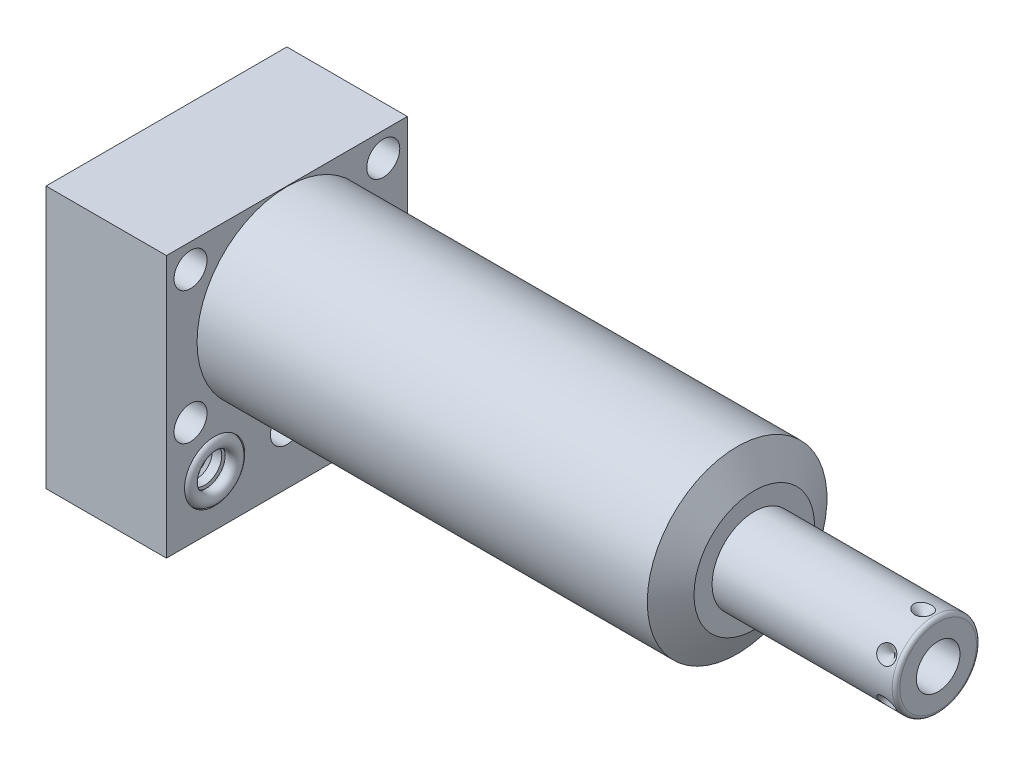
SolidWorks part; units mm, degrees
material "Alloy Steel"
ref_plane "Front Plane" through (0, 0, 0) normal (0, 0, 1) x (1, 0, 0)
ref_plane "Top Plane" through (0, 0, 0) normal (0, 1, 0) x (1, 0, 0)
ref_plane "Right Plane" through (0, 0, 0) normal (1, 0, 0) x (0, 0, -1)
ref_plane "Plane1" through (0, 0, 0) normal (1, 0, 0) x (0, 0, -1)
sketch "Sketch1" plane through (0, 0, 0) normal (1, 0, 0) x (0, 0, -1)
  line L0 (-31.75, 23.8252) -> (-31.75, -45.2628)
  line L1 (-31.75, -45.2628) -> (31.75, -45.2628)
  line L2 (31.75, -45.2628) -> (31.75, 23.8252)
  line L3 (31.75, 23.8252) -> (-31.75, 23.8252)
  line L4 (0, -55.6514) -> (0, 27.6098) construction
  dimension "D1" = 63.5
  dimension "D2" = 69.088
  dimension "D3" = 23.8252
extrude "Extrude1" add sketch "Sketch1" along normal blind 123.19 and the other way blind 31.75
ref_plane "Plane2" through (0, 0, 0) normal (1, 0, 0) x (0, 0, -1)
sketch "Sketch2" plane through (0, 0, 0) normal (1, 0, 0) x (0, 0, -1)
  line L0 (-26.0541, 0) -> (26.0541, 0) construction
  line L5 (31.75, 23.8252) -> (-31.75, 23.8252)
  line L6 (-31.75, 23.8252) -> (-31.75, -45.2628)
  line L7 (-31.75, -45.2628) -> (31.75, -45.2628)
  line L8 (31.75, -45.2628) -> (31.75, 23.8252)
  line L9 (31.75, 23.8252) -> (-31.75, 23.8252)
  line L10 (-31.75, 23.8252) -> (-31.75, -45.2628)
  line L11 (-31.75, -45.2628) -> (31.75, -45.2628)
  line L12 (31.75, -45.2628) -> (31.75, 23.8252)
  circle A0 centre (0, 0) radius 23.6855
  dimension "D1" = 47.371
  dimension "D2" = 0
extrude "Cut-Extrude1" cut sketch "Sketch2" along normal up to next
ref_plane "Plane3" through (0, 0, 0) normal (0, 0, 1) x (1, 0, 0)
sketch "Sketch3" plane through (0, 0, 0) normal (0, 0, 1) x (1, 0, 0)
  line L0 (118.6806, 23.6855) -> (123.19, 15.875)
  line L1 (76.0371, 0) -> (80.9975, 0) construction
  line L2 (123.19, 23.6855) -> (123.19, 15.875)
  line L3 (123.19, 23.6855) -> (118.6806, 23.6855)
  line L4 (123.19, 23.6855) -> (0, 23.6855) construction
  line L5 (123.19, -23.6855) -> (123.19, 23.6855) construction
  dimension "D1" = 31.75
  dimension "D2" = 30
revolve "Cut-Revolve1" cut sketch "Sketch3" angle 360 about L1
ref_plane "Plane4" through (-29.083, -31.75, 19.05) normal (0, 0, 1) x (0, 1, 0)
sketch "S2D0002" plane through (-29.083, -31.75, 19.05) normal (0, 0, 1) x (0, 1, 0)
  line L0 (0, 0) -> (4.5466, 0)
  line L1 (4.5466, 0) -> (4.1066, -2.0701)
  line L2 (4.1066, -2.0701) -> (3.4544, -2.7223)
  line L3 (3.4544, -2.7223) -> (3.4544, -13.97)
  line L4 (3.4544, -13.97) -> (0, -13.97)
  line L5 (0, -13.97) -> (0, 0)
  line L6 (0, -14.6685) -> (0, 0.6985) construction
  dimension "D1" = 13.97
revolve "Cut-Revolve2" cut sketch "S2D0002" angle 360 about L6
ref_plane "Plane5" through (-29.083, -31.75, -19.05) normal (0, 0, 1) x (0, 1, 0)
sketch "Sketch5" plane through (-29.083, -31.75, -19.05) normal (0, 0, 1) x (0, 1, 0)
  line L0 (0, 0) -> (4.5466, 0)
  line L1 (4.5466, 0) -> (4.1066, -2.0701)
  line L2 (4.1066, -2.0701) -> (3.4544, -2.7223)
  line L3 (3.4544, -2.7223) -> (3.4544, -13.97)
  line L4 (3.4544, -13.97) -> (0, -13.97)
  line L5 (0, -13.97) -> (0, 0)
  line L6 (0, -14.6685) -> (0, 0.6985) construction
  dimension "D1" = 13.97
revolve "Cut-Revolve3" cut sketch "Sketch5" angle 360 about L6
ref_plane "Plane6" through (-2.667, -31.75, 19.05) normal (0, 0, 1) x (0, -1, 0)
sketch "Sketch6" plane through (-2.667, -31.75, 19.05) normal (0, 0, 1) x (0, -1, 0)
  line L0 (0, 0) -> (4.5466, 0)
  line L1 (4.5466, 0) -> (4.1066, -2.0701)
  line L2 (4.1066, -2.0701) -> (3.4544, -2.7223)
  line L3 (3.4544, -2.7223) -> (3.4544, -12.192)
  line L4 (3.4544, -12.192) -> (0, -12.192)
  line L5 (0, -12.192) -> (0, 0)
  line L6 (0, -12.8016) -> (0, 0.6096) construction
  dimension "D1" = 12.192
revolve "Cut-Revolve4" cut sketch "Sketch6" angle 360 about L6
ref_plane "Plane7" through (-2.667, -31.75, -19.05) normal (0, 0, 1) x (0, -1, 0)
sketch "Sketch7" plane through (-2.667, -31.75, -19.05) normal (0, 0, 1) x (0, -1, 0)
  line L0 (0, 0) -> (4.5466, 0)
  line L1 (4.5466, 0) -> (4.1066, -2.0701)
  line L2 (4.1066, -2.0701) -> (3.4544, -2.7223)
  line L3 (3.4544, -2.7223) -> (3.4544, -12.192)
  line L4 (3.4544, -12.192) -> (0, -12.192)
  line L5 (0, -12.192) -> (0, 0)
  line L6 (0, -12.8016) -> (0, 0.6096) construction
  dimension "D1" = 12.192
revolve "Cut-Revolve5" cut sketch "Sketch7" angle 360 about L6
ref_plane "Plane8" through (-15.875, -51.6128, 19.05) normal (0, 0, 1) x (-1, 0, 0)
sketch "Sketch8" plane through (-15.875, -51.6128, 19.05) normal (0, 0, 1) x (-1, 0, 0)
  line L0 (0, -6.604) -> (6.1849, -6.604)
  line L1 (6.1849, -6.604) -> (5.6423, -9.1567)
  line L2 (5.6423, -9.1567) -> (4.9784, -9.8206)
  line L3 (4.9784, -9.8206) -> (4.9784, -25.654)
  line L4 (4.9784, -25.654) -> (0, -25.654)
  line L5 (0, -25.654) -> (0, -6.604)
  line L6 (0, -26.67) -> (0, 1.27) construction
  line L7 (15.875, -6.35) -> (-15.875, -6.35) construction
  dimension "D1" = 19.05
  dimension "D2" = 0.254
revolve "Cut-Revolve6" cut sketch "Sketch8" angle 360 about L6
ref_plane "Plane9" through (-15.875, -51.6128, -19.05) normal (0, 0, 1) x (-1, 0, 0)
sketch "Sketch9" plane through (-15.875, -51.6128, -19.05) normal (0, 0, 1) x (-1, 0, 0)
  line L0 (0, -6.604) -> (6.1849, -6.604)
  line L1 (6.1849, -6.604) -> (5.6423, -9.1567)
  line L2 (5.6423, -9.1567) -> (4.9784, -9.8206)
  line L3 (4.9784, -9.8206) -> (4.9784, -25.654)
  line L4 (4.9784, -25.654) -> (0, -25.654)
  line L5 (0, -25.654) -> (0, -6.604)
  line L6 (0, -26.67) -> (0, 1.27) construction
  line L7 (15.875, -6.35) -> (-15.875, -6.35) construction
  dimension "D1" = 19.05
  dimension "D2" = 0.254
revolve "Cut-Revolve7" cut sketch "Sketch9" angle 360 about L6
ref_plane "Plane10" through (0, 0, 0) normal (0, 0, 1) x (1, 0, 0)
sketch "Sketch18" plane through (0, 0, 0) normal (1, 0, 0) x (0, 0, -1)
  circle A0 centre (-19.05, -31.75) radius 7.9375
  circle A1 centre (19.05, -31.75) radius 7.9375
  dimension "D1" = 15.875
extrude "Cut-Extrude2" cut sketch "Sketch18" against normal blind 2.667
sketch "Sketch19" plane through (-31.75, 0, 0) normal (-1, 0, 0) x (0, 0, 1)
  circle A0 centre (-19.05, -31.75) radius 7.9375
  circle A1 centre (19.05, -31.75) radius 7.9375
  dimension "D1" = 15.875
extrude "Cut-Extrude3" cut sketch "Sketch19" against normal blind 2.667
sketch "Sketch20" plane through (0, -45.2628, 0) normal (0, -1, 0) x (1, 0, 0)
  circle A0 centre (-15.875, -19.05) radius 9.525
  circle A1 centre (-15.875, 19.05) radius 9.525
  circle A2 centre (-15.875, 19.05) radius 6.1849 construction
  dimension "D1" = 19.05
extrude "Cut-Extrude4" cut sketch "Sketch20" against normal blind 0.254
sketch "Sketch10" plane through (0, 0, 0) normal (0, 0, 1) x (1, 0, 0)
  line L0 (123.19, 0) -> (123.19, 11.1125)
  line L1 (123.19, 11.1125) -> (170.6626, 11.1125)
  line L2 (171.6786, 10.0965) -> (171.6786, 0)
  line L3 (171.6786, 0) -> (123.19, 0)
  line L4 (58.2708, 0) -> (120.537, 0) construction
  line L5 (123.19, -15.875) -> (123.19, 15.875) construction
  line L6 (-31.75, 23.8252) -> (-31.75, -45.2628) construction
  arc A0 (171.6786, 10.0965) -> (170.6626, 11.1125) centre (170.6626, 10.0965) ccw
  point P0 (80.772, 0)
  dimension "D2" = 1.016
  dimension "D1" = 22.225
  dimension "D3" = 203.4286
revolve "Revolve1" add sketch "Sketch10" angle 360 about L4
ref_plane "Plane11" through (118.6434, -5.7531, 0) normal (0, 0, 1) x (0, -1, 0)
sketch "S2D0001" plane through (118.6434, -5.7531, 0) normal (0, 0, 1) x (0, -1, 0)
  line L0 (0, 53.0352) -> (0, 36.0172)
  line L1 (0, 36.0172) -> (-5.7531, 32.5604)
  line L2 (0, 53.0352) -> (-5.7531, 53.0352)
  line L3 (-5.7531, 53.0352) -> (-5.7531, 32.5604)
  line L4 (-5.7531, -34.3471) -> (-5.7531, 1.0237) construction
  line L5 (4.3434, 53.0352) -> (-15.8496, 53.0352) construction
  dimension "D1" = 11.5062
  dimension "D2" = 17.018
  dimension "D3" = 59
revolve "Cut-Revolve8" cut sketch "S2D0001" angle 360 about L4
ref_plane "Plane14" through (0, -31.75, -19.05) normal (0, -1, 0) x (0, 0, -1)
sketch "Sketch14" plane through (0, -31.75, -19.05) normal (0, -1, 0) x (0, 0, -1)
  line L0 (0, -2.8435) -> (0, 1.0401) construction
  line L1 (0, -5.3893) -> (0, -12.2901) construction
  line L2 (7.9375, -2.667) -> (-7.9375, -2.667) construction
  circle A0 centre (6.1722, -0.9017) radius 1.7653
  dimension "D1" = 3.5306
  dimension "D2" = 12.3444
revolve "Revolve2" add sketch "Sketch14" angle 360 about L0
ref_plane "Plane15" through (0, -31.75, -19.05) normal (0, -1, 0) x (0, 0, -1)
sketch "Sketch15" plane through (0, -31.75, -19.05) normal (0, -1, 0) x (0, 0, -1)
  line L0 (0, -32.7901) -> (0, -28.9065) construction
  line L1 (0, -29.083) -> (0, -27.0129) construction
  line L2 (-7.9375, -29.083) -> (7.9375, -29.083) construction
  circle A0 centre (6.1722, -30.8483) radius 1.7653
  dimension "D1" = 3.5306
  dimension "D2" = 12.3444
revolve "Revolve3" add sketch "Sketch15" angle 360 about L0
ref_plane "Plane16" through (114.681, -11.1125, 0) normal (0, 0, 1) x (-1, 0, 0)
sketch "Sketch16" plane through (114.681, -11.1125, 0) normal (0, 0, 1) x (-1, 0, 0)
  line L0 (-53.0352, 0) -> (-50.6222, 0)
  line L1 (-50.6222, 0) -> (-53.0352, -2.413)
  line L2 (-53.0352, 0) -> (-53.0352, -2.413)
  line L3 (-53.0352, -5.0193) -> (-53.0352, 0.1207) construction
  line L4 (-8.509, 0) -> (-55.9816, 0) construction
  line L5 (-56.9976, -1.016) -> (-56.9976, -21.209) construction
  dimension "D1" = 3.9624
  dimension "D2" = 4.826
  dimension "D3" = 45
ref_plane "Plane17" through (114.681, 11.1125, 0) normal (0, 0, 1) x (1, 0, 0)
revolve "Cut-Revolve9" cut sketch "Sketch16" angle 360 about L3
pattern_circular "CirPattern1" count 6 over 360 of "Cut-Revolve9"
hole_wizard "Hole1" positions "Sketch22" profile "Sketch21" legacy end condition up to next
sketch "Sketch22" plane through (0, 0, 0) normal (1, 0, 0) x (0, 0, -1)
  line L0 (0, 0) -> (-38.8053, 0) construction
  line L1 (0, 0) -> (0, 31.2017) construction
  point P0 (-25.4, 17.4752)
  point P1 (0, -30.8356)
  point P12 (-25.4, -17.4752)
  point P14 (25.4, 17.4752)
  point P15 (25.4, -17.4752)
  dimension "D1" = 25.4
  dimension "D2" = 17.4752
  dimension "D3" = 30.8356
sketch "Sketch21" plane through (0, 17.4752, 25.4) normal (0, 1, 0) x (0, 0, -1)
  line L0 (0, 0) -> (0, 31.75)
  line L1 (0, 31.75) -> (4.3561, 31.75)
  line L2 (4.3561, 31.75) -> (4.3561, 0)
  line L3 (4.3561, 0) -> (0, 0)
  line L4 (0, 110) -> (0, -10) construction
  dimension "Diameter" = 8.7122
  dimension "Depth" = 31.75
pattern_linear "LPattern1" count 2 spacing 38.1 along (0, 0, 1) of "Revolve2", "Revolve3"
